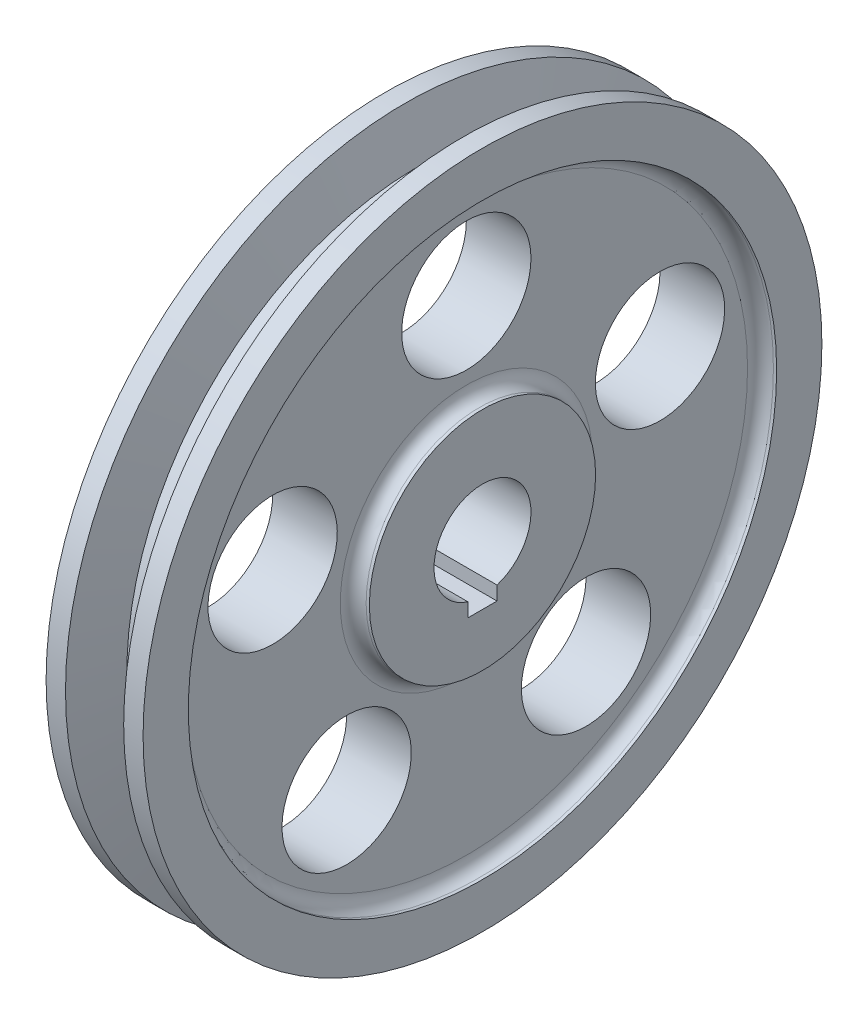
SolidWorks part; units mm, degrees
ref_plane "Front Plane" through (0, 0, 0) normal (0, 0, 1) x (1, 0, 0)
ref_plane "Top Plane" through (0, 0, 0) normal (0, 1, 0) x (1, 0, 0)
ref_plane "Right Plane" through (0, 0, 0) normal (1, 0, 0) x (0, 0, -1)
sketch "Sketch1" plane through (0, 0, 0) normal (0, 0, 1) x (1, 0, 0)
  line L0 (-7.5, 7.5) -> (7.5, 7.5)
  line L1 (-7.5, 7.5) -> (-7.5, 17.5)
  line L2 (0, 0) -> (0, 97.5393) construction
  line L3 (-7.5, 17.5) -> (-7, 17.5)
  line L4 (-5, 19.5) -> (-5, 43.5)
  line L5 (-7, 45.5) -> (-7.5, 45.5)
  line L6 (-7.5, 45.5) -> (-7.5, 52.5)
  line L7 (-7.5, 52.5) -> (-4.5, 52.5)
  line L8 (-4.5, 52.5) -> (-2.5, 45)
  line L9 (-2.5, 45) -> (2.5, 45)
  line L10 (4.5, 52.5) -> (2.5, 45)
  line L11 (7.5, 52.5) -> (4.5, 52.5)
  line L12 (7.5, 45.5) -> (7.5, 52.5)
  line L13 (7, 45.5) -> (7.5, 45.5)
  line L14 (5, 19.5) -> (5, 43.5)
  line L15 (7.5, 17.5) -> (7, 17.5)
  line L16 (7.5, 7.5) -> (7.5, 17.5)
  arc A0 (-5, 43.5) -> (-7, 45.5) centre (-7, 43.5) ccw
  arc A1 (-7, 17.5) -> (-5, 19.5) centre (-7, 19.5) ccw
  arc A2 (5, 43.5) -> (7, 45.5) centre (7, 43.5) cw
  arc A3 (7, 17.5) -> (5, 19.5) centre (7, 19.5) cw
  point P18 (0, 45)
  point P29 (0, 7.5)
  dimension "D1" = 2
  dimension "D2" = 7.5
  dimension "D3" = 7.5
  dimension "D4" = 5
  dimension "D5" = 45
  dimension "D6" = 45
  dimension "D7" = 10
  dimension "D8" = 7
  dimension "D10" = 2.5
  dimension "D11" = 7.5
ref_axis "Axis1" through (25.864, 0, 0) along (-1, 0, 0)
revolve "Revolve1" add sketch "Sketch1" angle 360 about axis through (25.864, 0, 0) along (-1, 0, 0)
sketch "Sketch2" plane through (5, 0, 0) normal (1, 0, 0) x (0, 0, -1)
  line L0 (0, 43.5) -> (0, 19.5) construction
  circle A0 centre (0, 0) radius 43.5 construction
  circle A1 centre (0, 0) radius 19.5 construction
  circle A2 centre (0, 31.5) radius 10
  point P2 (0, 31.5)
  dimension "D1" = 20
extrude "Extrude1" cut sketch "Sketch2" against normal blind 10
pattern_circular "CirPattern1" count 5 over 360 about axis through (0, 0, 0) along (1, 0, 0) of "Extrude1"
sketch "Sketch3" plane through (7.5, 0, 0) normal (1, 0, 0) x (0, 0, -1)
  line L1 (-2.25, -7) -> (2.25, -7)
  line L2 (-2.25, -7) -> (-2.25, -9.3)
  line L3 (-2.25, -9.3) -> (2.25, -9.3)
  line L4 (2.25, -7) -> (2.25, -9.3)
  point P4 (0, -7)
  dimension "D1" = 2.3
  dimension "D2" = 4.5
  dimension "D3" = 7
extrude "Extrude2" cut sketch "Sketch3" against normal through all
